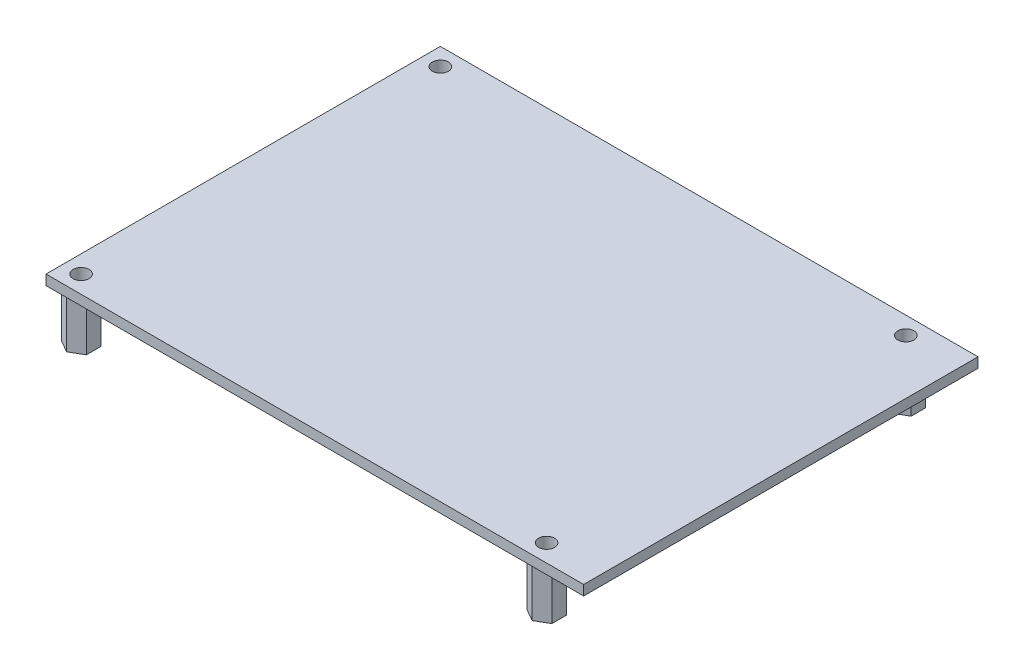
SolidWorks part; units mm, degrees
ref_plane "Спереди" through (0, 0, 0) normal (0, 0, 1) x (1, 0, 0)
ref_plane "Сверху" through (0, 0, 0) normal (0, 1, 0) x (1, 0, 0)
ref_plane "Справа" through (0, 0, 0) normal (1, 0, 0) x (0, 0, -1)
sketch "Эскиз1" plane through (0, 0, 0) normal (0, 1, 0) x (1, 0, 0)
  line L0 (0, 0) -> (107.3, 0)
  line L1 (0, 0) -> (0, 78.7)
  line L2 (107.3, 0) -> (107.3, 78.7)
  line L3 (0, 78.7) -> (107.3, 78.7)
  line L4 (3.5, 75.2) -> (96.4, 75.2) construction
  line L5 (3.5, 75.2) -> (3.5, 3.5) construction
  line L6 (96.4, 75.2) -> (96.4, 3.5) construction
  line L7 (3.5, 3.5) -> (96.4, 3.5) construction
  circle A0 centre (3.5, 75.2) radius 1.6
  circle A1 centre (96.4, 75.2) radius 1.6
  circle A2 centre (96.4, 3.5) radius 1.6
  circle A3 centre (3.5, 3.5) radius 1.6
  dimension "D7" = 3.2
  dimension "D8" = 3.2
  dimension "D9" = 3.2
  dimension "D10" = 3.2
  dimension "D1" = 78.7
  dimension "D2" = 107.3
  dimension "D3" = 3.5
  dimension "D4" = 3.5
  dimension "D5" = 71.7
  dimension "D6" = 92.9
  dimension "D11" = 3.5
extrude "Бобышка-Вытянуть1" add sketch "Эскиз1" along normal blind 2
sketch "Эскиз2" plane through (0, 0, 0) normal (0, -1, 0) x (1, 0, 0)
  line L0 (3.5, -3.5) -> (96.4, -3.5) construction
  line L1 (93.9, -4.9434) -> (96.4, -6.3868)
  line L2 (96.4, -6.3868) -> (98.9, -4.9434)
  line L3 (98.9, -4.9434) -> (98.9, -2.0566)
  line L4 (98.9, -2.0566) -> (96.4, -0.6132)
  line L5 (96.4, -0.6132) -> (93.9, -2.0566)
  line L6 (93.9, -2.0566) -> (93.9, -4.9434)
  line L7 (93.9, -76.6434) -> (96.4, -78.0868)
  line L8 (96.4, -78.0868) -> (98.9, -76.6434)
  line L9 (98.9, -76.6434) -> (98.9, -73.7566)
  line L10 (98.9, -73.7566) -> (96.4, -72.3132)
  line L11 (96.4, -72.3132) -> (93.9, -73.7566)
  line L12 (93.9, -73.7566) -> (93.9, -76.6434)
  line L13 (3.5, -6.3868) -> (6, -4.9434)
  line L14 (6, -4.9434) -> (6, -2.0566)
  line L15 (6, -2.0566) -> (3.5, -0.6132)
  line L16 (3.5, -0.6132) -> (1, -2.0566)
  line L17 (1, -2.0566) -> (1, -4.9434)
  line L18 (1, -4.9434) -> (3.5, -6.3868)
  line L19 (3.5, -72.3132) -> (1, -73.7566)
  line L20 (1, -73.7566) -> (1, -76.6434)
  line L21 (1, -76.6434) -> (3.5, -78.0868)
  line L22 (3.5, -78.0868) -> (6, -76.6434)
  line L23 (6, -76.6434) -> (6, -73.7566)
  line L24 (6, -73.7566) -> (3.5, -72.3132)
  line L25 (3.5, -3.5) -> (3.5, -75.2) construction
  line L26 (96.4, -3.5) -> (96.4, -75.2) construction
  line L27 (3.5, -75.2) -> (96.4, -75.2) construction
  circle A0 centre (96.4, -3.5) radius 2.5 construction
  circle A1 centre (96.4, -75.2) radius 2.5 construction
  circle A2 centre (3.5, -3.5) radius 2.5 construction
  circle A3 centre (3.5, -75.2) radius 2.5 construction
  dimension "D1" = 5
  dimension "D2" = 5
  dimension "D3" = 5
  dimension "D4" = 5
extrude "Бобышка-Вытянуть2" add sketch "Эскиз2" along normal blind 10
sketch "Эскиз3" plane through (0, 0, 0) normal (0, 1, 0) x (1, 0, 0)
  circle A1 centre (3.5, 3.5) radius 1.6
  circle A2 centre (3.5, 3.5) radius 1.6
  circle A3 centre (3.5, 75.2) radius 1.6
  circle A4 centre (3.5, 75.2) radius 1.6
  circle A5 centre (96.4, 75.2) radius 1.6
  circle A6 centre (96.4, 75.2) radius 1.6
  circle A7 centre (96.4, 3.5) radius 1.6
  circle A8 centre (96.4, 3.5) radius 1.6
  dimension "D1" = 0
  dimension "D2" = 0
  dimension "D3" = 0
  dimension "D4" = 0
extrude "Вырез-Вытянуть1" cut sketch "Эскиз3" against normal through all
sketch "Эскиз5" plane through (0, 2, 0) normal (0, 1, 0) x (1, 0, 0)
  line L0 (0, 39.35) -> (107.3, 39.35) construction
  line L1 (0, 78.7) -> (0, 0) construction
  line L2 (107.3, 0) -> (107.3, 78.7) construction
  line L3 (3.5, 75.2) -> (3.5, 3.5) construction
ref_plane "Плоскость1" through (0, 0, -39.35) normal (0, 0, 1) x (1, 0, 0)
ref_plane "Плоскость2" through (3.5, 0, 0) normal (-1, 0, 0) x (0, 0, 1)
sketch "Sketch1" plane through (0, 0, -78.7) normal (0, 0, -1) x (-1, 0, 0)
  line L0 (-82.3, 0) -> (-82.3, 15) construction
  line L1 (-107.3, 0) -> (0, 0) construction
  line L2 (-82.3, 15) -> (-72.3, 15) construction
  line L3 (-72.3, 15) -> (-72.3, 0) construction
  line L4 (-72.3, 0) -> (-82.3, 0) construction
  line L5 (-92.3, 0) -> (-92.3, 15) construction
  line L6 (-92.3, 15) -> (-82.3, 15) construction
  dimension "D1" = 15
  dimension "D2" = 25
  dimension "D3" = 10
  dimension "D4" = 10
